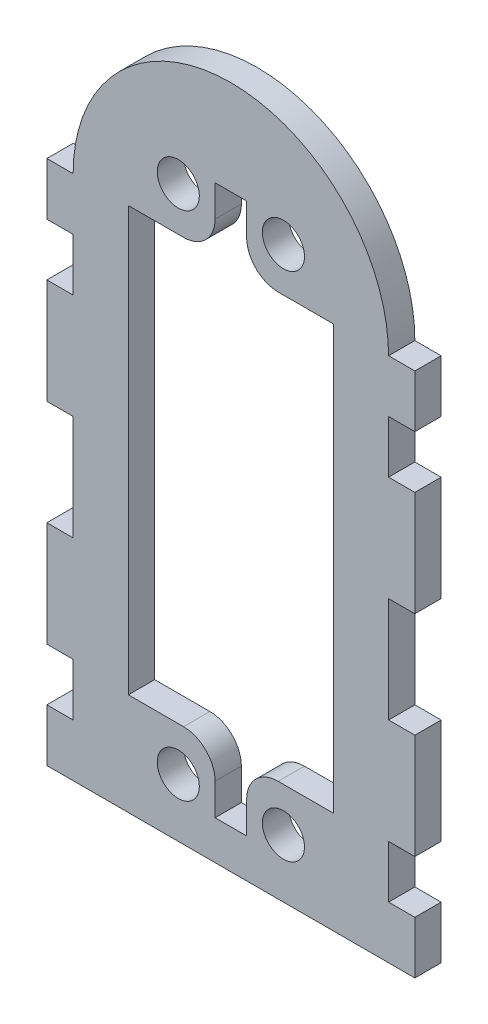
SolidWorks part; units mm, degrees
ref_plane "Alzado" through (0, 0, 0) normal (0, 0, 1) x (1, 0, 0)
ref_plane "Planta" through (0, 0, 0) normal (0, 1, 0) x (1, 0, 0)
ref_plane "Vista lateral" through (0, 0, 0) normal (1, 0, 0) x (0, 0, -1)
sketch "Croquis1" plane through (0, 0, 0) normal (0, 0, 1) x (1, 0, 0)
  line L0 (-15, -54.9999) -> (-15, -58) construction
  line L1 (-9.75, 20.15) -> (-1.5, 20.15)
  line L2 (-9.75, 20.15) -> (-9.75, -20.15)
  line L3 (-9.75, -20.15) -> (-1.5, -20.15)
  line L4 (9.75, 20.15) -> (9.75, -20.15)
  line L5 (-9.75, 20.15) -> (9.75, -20.15) construction
  line L6 (-9.75, -20.15) -> (9.75, 20.15) construction
  line L7 (1.5, 20.15) -> (9.75, 20.15)
  line L8 (-15, 20.15) -> (-15, -51.9999) construction
  line L9 (-15, -58) -> (15, -58) construction
  line L10 (15, 20.15) -> (15, -51.9986) construction
  line L11 (-15, -54.9999) -> (-18, -54.9999) construction
  line L12 (-18, -54.9999) -> (-15, -51.9999) construction
  line L13 (15, -54.9986) -> (15, -58) construction
  line L14 (15, -51.9986) -> (18, -54.9986) construction
  line L15 (18, -54.9986) -> (15, -54.9986) construction
  line L16 (-1.5, 26.15) -> (1.5, 26.15)
  line L17 (-1.5, 26.15) -> (-1.5, 20.15)
  line L18 (1.5, -20.15) -> (9.75, -20.15)
  line L19 (1.5, 26.15) -> (1.5, 20.15)
  line L20 (-1.5, 26.15) -> (1.5, 20.15) construction
  line L21 (-1.5, 20.15) -> (1.5, 26.15) construction
  line L22 (-1.5, -26.15) -> (1.5, -26.15)
  line L23 (-1.5, -26.15) -> (-1.5, -20.15)
  line L24 (-15, 20.15) -> (-17.5, 20.15)
  line L25 (1.5, -26.15) -> (1.5, -20.15)
  line L26 (-1.5, -26.15) -> (1.5, -20.15) construction
  line L27 (-1.5, -20.15) -> (1.5, -26.15) construction
  line L28 (-15, -29.85) -> (15, -29.85)
  line L29 (-17.5, 20.15) -> (-17.5, 15.15)
  line L30 (-17.5, 15.15) -> (-15, 15.15)
  line L31 (-15, 15.15) -> (-15, 10.15)
  line L32 (-15, 10.15) -> (-17.5, 10.15)
  line L33 (-17.5, 10.15) -> (-17.5, 0.15)
  line L34 (-17.5, 0.15) -> (-15, 0.15)
  line L35 (-15, 0.15) -> (-15, -9.85)
  line L36 (-15, -9.85) -> (-17.5, -9.85)
  line L37 (-17.5, -9.85) -> (-17.5, -19.85)
  line L38 (-17.5, -19.85) -> (-15, -19.85)
  line L39 (-15, -19.85) -> (-15, -24.85)
  line L40 (-15, -24.85) -> (-17.5, -24.85)
  line L41 (-17.5, -24.85) -> (-17.5, -29.85)
  line L42 (-17.5, -29.85) -> (-15, -29.85)
  line L43 (15, 20.15) -> (17.5, 20.15)
  line L44 (17.5, 20.15) -> (17.5, 15.15)
  line L45 (17.5, 15.15) -> (15, 15.15)
  line L46 (15, 15.15) -> (15, 10.15)
  line L47 (15, 10.15) -> (17.5, 10.15)
  line L48 (17.5, 10.15) -> (17.5, 0.15)
  line L49 (17.5, 0.15) -> (15, 0.15)
  line L50 (15, 0.15) -> (15, -9.85)
  line L51 (15, -9.85) -> (17.5, -9.85)
  line L52 (17.5, -9.85) -> (17.5, -19.85)
  line L53 (17.5, -19.85) -> (15, -19.85)
  line L54 (15, -19.85) -> (15, -24.85)
  line L55 (15, -24.85) -> (17.5, -24.85)
  line L56 (17.5, -24.85) -> (17.5, -29.85)
  line L57 (17.5, -29.85) -> (15, -29.85)
  circle A0 centre (-5, 24.315) radius 2
  circle A1 centre (5, 24.315) radius 2
  circle A2 centre (-5, -24.315) radius 2
  circle A3 centre (5, -24.315) radius 2
  arc A4 (-15, 20.15) -> (15, 20.15) centre (0, 20.15) cw
  point P0 (0, 0)
  point P19 (0, 23.15)
  point P30 (0, -23.15)
  dimension "D3" = 4.75
  dimension "D4" = 4.165
  dimension "D7" = 4
  dimension "D8" = 4
  dimension "D12" = 4
  dimension "D13" = 4
  dimension "D21" = 15
  dimension "D1" = 40.3
  dimension "D2" = 19.5
  dimension "D5" = 10
  dimension "D6" = 4.165
  dimension "D10" = 4.165
  dimension "D11" = 10
  dimension "D14" = 4.75
  dimension "D15" = 5.25
  dimension "D16" = 50
  dimension "D17" = 78.15
  dimension "D18" = 6
  dimension "D19" = 3
  dimension "D20" = 3.5
  dimension "D25" = 3
  dimension "D26" = 3.5
extrude "Saliente-Extruir1" add sketch "Croquis1" along normal blind 2.5
fillet "Redondeo6" radius 3 1 edges at (-1.5, -20.15, 1.25)
fillet "Redondeo7" radius 3 1 edges at (1.5, -20.15, 1.25)
fillet "Redondeo8" radius 3 2 edges at (1.5, 20.15, 1.25) (-1.5, 20.15, 1.25)
